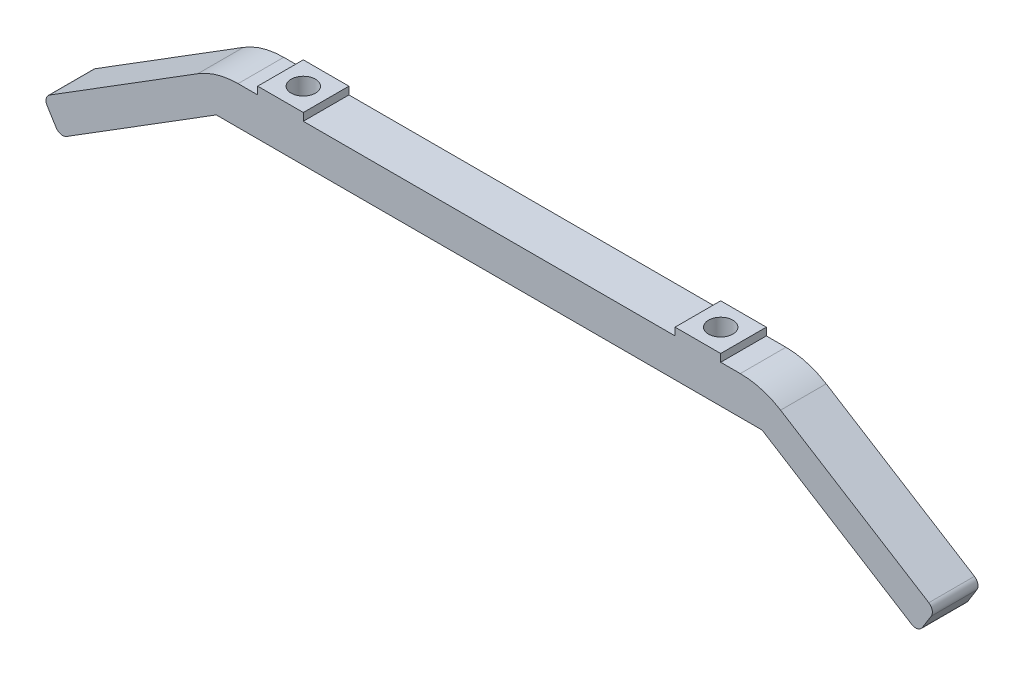
SolidWorks part; units mm, degrees
ref_plane "前视基准面" through (0, 0, 0) normal (0, 0, 1) x (1, 0, 0)
ref_plane "上视基准面" through (0, 0, 0) normal (0, 1, 0) x (1, 0, 0)
ref_plane "右视基准面" through (0, 0, 0) normal (1, 0, 0) x (0, 0, -1)
sketch "草图1" plane through (0, 0, 0) normal (0, 0, 1) x (1, 0, 0)
  line L0 (0, 148.5) -> (0, -94.9538) construction
  line L1 (105, -148.5) -> (-105, -148.5) construction
  line L2 (105, -148.5) -> (105, 148.5) construction
  line L3 (105, 148.5) -> (-105, 148.5) construction
  line L4 (-105, -148.5) -> (-105, 148.5) construction
  line L5 (105, -148.5) -> (-105, 148.5) construction
  line L6 (105, 148.5) -> (-105, -148.5) construction
  line L7 (35.8892, 121.6645) -> (-35.8892, 121.6645)
  line L8 (-35.8892, 121.6645) -> (-66.9017, 102.292)
  line L9 (-75, 40.9339) -> (-75, 31.2613)
  line L10 (-66.9017, 102.292) -> (-66.9017, 52.8701)
  line L11 (75, 40.9339) -> (75, 31.2613)
  line L12 (66.9017, 102.292) -> (66.9017, 52.8701)
  line L13 (35.8892, 121.6645) -> (66.9017, 102.292)
  line L14 (-75, 31.2613) -> (75, 31.2613)
  line L15 (-60, -148.5) -> (-60, -91.8129)
  line L16 (-75, 23.94) -> (75, 23.94)
  line L17 (-75, 23.94) -> (-75, 10.5626)
  line L18 (-38.8455, -105.5906) -> (-66.4608, -113.7617)
  line L19 (-66.4608, -113.7617) -> (-70.1743, -102.7328)
  line L20 (75, 23.94) -> (75, 10.5626)
  line L21 (66.4608, -113.7617) -> (70.1743, -102.7328)
  line L22 (38.8455, -105.5906) -> (66.4608, -113.7617)
  line L23 (-105, 93.0519) -> (105, 93.0519)
  line L24 (-105, 63.0519) -> (105, 63.0519)
  line L25 (-105, -90.0629) -> (-70.5337, -90.0629)
  line L26 (-105, -60.0629) -> (-67.4027, -60.0629)
  line L27 (60, -148.5) -> (60, 148.5)
  line L28 (-60, -58.3129) -> (-45, -58.3129)
  line L29 (-60, -61.8129) -> (-45, -61.8129)
  line L30 (-36, -58.3129) -> (-21, -58.3129)
  line L31 (-36, -61.8129) -> (-21, -61.8129)
  line L32 (-60, -88.3129) -> (-45, -88.3129)
  line L33 (-60, -91.8129) -> (-45, -91.8129)
  line L34 (-36, -88.3129) -> (-21, -88.3129)
  line L35 (-36, -91.8129) -> (-21, -91.8129)
  line L36 (-60, -58.3129) -> (-60, 148.5)
  line L37 (-19.25, -90.0629) -> (105, -90.0629)
  line L38 (-19.25, -60.0629) -> (19.25, -60.0629)
  line L39 (-60, -88.3129) -> (-60, -61.8129)
  line L40 (21, -58.3129) -> (36, -58.3129)
  line L41 (45, -58.3129) -> (60, -58.3129)
  line L42 (60, -61.8129) -> (45, -61.8129)
  line L43 (36, -61.8129) -> (21, -61.8129)
  line L44 (21, -88.3129) -> (36, -88.3129)
  line L45 (21, -91.8129) -> (36, -91.8129)
  line L46 (45, -88.3129) -> (60, -88.3129)
  line L47 (45, -91.8129) -> (60, -91.8129)
  line L48 (37.75, -60.0629) -> (43.25, -60.0629)
  line L49 (58.25, -60.0629) -> (105, -60.0629)
  line L50 (-60, 94.8019) -> (-45, 94.8019)
  line L51 (-36, 94.8019) -> (-21, 94.8019)
  line L52 (-60, 91.3019) -> (-45, 91.3019)
  line L53 (-36, 91.3019) -> (-21, 91.3019)
  line L54 (-60, 64.8019) -> (-45, 64.8019)
  line L55 (-60, 61.3019) -> (-45, 61.3019)
  line L56 (-36, 64.8019) -> (-21, 64.8019)
  line L57 (-36, 61.3019) -> (-21, 61.3019)
  line L58 (21, 94.8019) -> (36, 94.8019)
  line L59 (21, 91.3019) -> (36, 91.3019)
  line L60 (45, 94.8019) -> (60, 94.8019)
  line L61 (45, 91.3019) -> (60, 91.3019)
  line L62 (21, 61.3019) -> (36, 61.3019)
  line L63 (21, 64.8019) -> (36, 64.8019)
  line L64 (45, 61.3019) -> (60, 61.3019)
  line L65 (45, 64.8019) -> (60, 64.8019)
  line L66 (-33.1709, -104.7687) -> (33.1709, -104.7687)
  line L67 (0, -104.7687) -> (0, -148.5) construction
  arc A0 (-75, 40.9339) -> (-66.9017, 52.8701) centre (-79.7474, 52.8701) ccw
  arc A1 (75, 40.9339) -> (66.9017, 52.8701) centre (79.7474, 52.8701) cw
  arc A3 (-60, -88.3129) -> (-60, -91.8129) centre (-60, -90.0629) ccw
  arc A4 (-60, -58.3129) -> (-60, -61.8129) centre (-60, -60.0629) ccw
  circle A5 centre (-60, 63.0519) radius 1.75
  circle A6 centre (-60, 93.0519) radius 1.75
  circle A7 centre (60, 93.0519) radius 1.75
  circle A8 centre (60, 63.0519) radius 1.75
  arc A9 (60, -91.8129) -> (60, -88.3129) centre (60, -90.0629) ccw
  arc A10 (60, -61.8129) -> (60, -58.3129) centre (60, -60.0629) ccw
  arc A11 (-36, -58.3129) -> (-36, -61.8129) centre (-36, -60.0629) ccw
  arc A12 (-36, -88.3129) -> (-36, -91.8129) centre (-36, -90.0629) ccw
  arc A13 (36, -61.8129) -> (36, -58.3129) centre (36, -60.0629) ccw
  arc A14 (36, -91.8129) -> (36, -88.3129) centre (36, -90.0629) ccw
  arc A15 (-45, -61.8129) -> (-45, -58.3129) centre (-45, -60.0629) ccw
  arc A16 (-21, -61.8129) -> (-21, -58.3129) centre (-21, -60.0629) ccw
  arc A17 (-45, -91.8129) -> (-45, -88.3129) centre (-45, -90.0629) ccw
  arc A18 (-21, -91.8129) -> (-21, -88.3129) centre (-21, -90.0629) ccw
  arc A19 (45, -58.3129) -> (45, -61.8129) centre (45, -60.0629) ccw
  arc A20 (21, -58.3129) -> (21, -61.8129) centre (21, -60.0629) ccw
  arc A21 (21, -88.3129) -> (21, -91.8129) centre (21, -90.0629) ccw
  arc A22 (45, -88.3129) -> (45, -91.8129) centre (45, -90.0629) ccw
  circle A23 centre (-36, 93.0519) radius 1.75
  circle A24 centre (-36, 63.0519) radius 1.75
  circle A25 centre (36, 93.0519) radius 1.75
  circle A26 centre (36, 63.0519) radius 1.75
  circle A27 centre (-45, 93.0519) radius 1.75
  circle A28 centre (-21, 93.0519) radius 1.75
  circle A29 centre (-45, 63.0519) radius 1.75
  circle A30 centre (-21, 63.0519) radius 1.75
  circle A31 centre (21, 93.0519) radius 1.75
  circle A32 centre (21, 63.0519) radius 1.75
  circle A33 centre (45, 93.0519) radius 1.75
  circle A34 centre (45, 63.0519) radius 1.75
  arc A35 (33.1709, -104.7687) -> (38.8455, -105.5906) centre (33.1709, -124.7687) cw
  arc A36 (-33.1709, -104.7687) -> (-38.8455, -105.5906) centre (-33.1709, -124.7687) ccw
  spline S0 degree 3 poles (-75, 10.5626) (-72.6959, 1.9073) (-70.3396, -13.3728) (-67.1028, -43.6255) (-66.7657, -72.9327) (-71.8903, -95.1489) (-70.1743, -102.7328) knots 0 0 0 0 0.235247 0.406294 0.801186 1 1 1 1
  spline S1 degree 3 poles (75, 10.5626) (72.6959, 1.9073) (70.3396, -13.3728) (67.1028, -43.6255) (66.7657, -72.9327) (71.8903, -95.1489) (70.1743, -102.7328) knots 0 0 0 0 0.235247 0.406294 0.801186 1 1 1 1
  point P0 (0, 0)
  point P27 (0, 121.6645)
  point P42 (0, -94.0966)
  dimension "D1" = 60
  dimension "D4" = 20
  dimension "D5" = 24
  dimension "D7" = 24
  dimension "D9" = 15
  dimension "D10" = 15
  dimension "D13" = 24
  dimension "D17" = 15
  dimension "D2" = 30
  dimension "D3" = 30
  dimension "D6" = 24
  dimension "D8" = 24
  dimension "D11" = 15
  dimension "D12" = 15
  dimension "D14" = 24
  dimension "D15" = 24
  dimension "D16" = 24
  dimension "D18" = 15
  dimension "D19" = 15
  dimension "D20" = 15
  dimension "D21" = 15
  dimension "D22" = 15
  dimension "D23" = 15
  dimension "D24" = 15
  dimension "D25" = 15
  dimension "D26" = 15
  dimension "D27" = 15
  dimension "D28" = 15
  dimension "D29" = 3.5
  dimension "D30" = 3.5
  dimension "D31" = 3.5
extrude "凸台-拉伸1" add sketch "草图1" along normal blind 3
sketch "草图7" plane through (0, 0, 0) normal (0, 0, -1) x (-1, 0, 0)
  line L0 (0, 121.6645) -> (0, -104.7687) construction
  line L1 (-35.8892, 121.6645) -> (35.8892, 121.6645) construction
  line L2 (33.1709, -104.7687) -> (-33.1709, -104.7687) construction
  line L3 (0, 41.2613) -> (-21, 41.2613) construction
  line L4 (0, 41.2613) -> (21, 41.2613) construction
  line L5 (0, 13.94) -> (-21, 13.94) construction
  line L6 (0, 13.94) -> (21, 13.94) construction
  line L7 (75, 23.94) -> (-75, 23.94) construction
  line L8 (75, 31.2613) -> (-75, 31.2613) construction
  circle A0 centre (-21, 41.2613) radius 2.25
  circle A1 centre (21, 41.2613) radius 2.25
  circle A2 centre (-21, 13.94) radius 2.25
  circle A3 centre (21, 13.94) radius 2.25
  dimension "D1" = 10
  dimension "D2" = 10
extrude "切除-拉伸2" cut sketch "草图7" against normal through all
sketch "草图8" plane through (0, 0, 3) normal (0, 0, 1) x (1, 0, 0)
  line L0 (0, 121.6645) -> (0, -1.9696) construction
  line L1 (35.8892, 121.6645) -> (-35.8892, 121.6645) construction
  line L2 (-33.1709, -104.7687) -> (33.1709, -104.7687) construction
  line L3 (-33.409, 20.409) -> (-12.6214, -0.3786)
  line L4 (31.818, -51.182) -> (-31.818, -51.182)
  line L5 (35, -48) -> (35, 15.6418)
  line L8 (-35, 18.818) -> (-12.6214, -3.5605) construction
  line L9 (-33.409, -52.773) -> (-12.5737, -31.9377)
  line L10 (-36.591, 17.227) -> (-15.8034, -3.5605)
  line L11 (33.4105, 20.4105) -> (12.573, -0.427)
  line L12 (15.803, -3.5609) -> (36.5881, 17.2241)
  line L13 (31.8195, 18.8195) -> (-31.818, 18.818)
  line L14 (-15.8038, -28.8038) -> (-36.591, -49.591)
  line L15 (12.5534, -31.9174) -> (33.409, -52.773)
  line L16 (34.9993, 18.8173) -> (12.6207, -3.5613) construction
  line L17 (0, -30.3951) -> (0, -104.7687) construction
  line L18 (-35, -48) -> (-35, 15.636)
  line L19 (-11.9624, -1.9696) -> (-14.2124, -1.9696) construction
  line L20 (15.8034, -28.8034) -> (36.591, -49.591)
  line L21 (14.2117, -30.3951) -> (11.9607, -30.3951) construction
  line L22 (14.2117, -30.3951) -> (14.2117, -28.1441) construction
  line L23 (14.2117, -1.9696) -> (11.9612, -1.9696) construction
  line L24 (-14.2124, -30.3951) -> (-14.2124, -28.1446) construction
  line L25 (14.2117, -30.3951) -> (12.62, -28.8034) construction
  line L26 (14.2117, -1.9696) -> (12.6204, -3.5609) construction
  line L27 (12.6207, -28.8027) -> (35, -51.182) construction
  line L28 (-12.6215, -3.5606) -> (-14.2124, -1.9696) construction
  line L29 (-14.2124, -4.2196) -> (-14.2124, -1.9696) construction
  line L30 (-12.6214, -28.8034) -> (-35, -51.182) construction
  line L31 (-12.6211, -28.8037) -> (-14.2124, -30.3951) construction
  line L32 (-11.9619, -30.3951) -> (-14.2124, -30.3951) construction
  line L33 (14.2117, -4.2201) -> (14.2117, -1.9696) construction
  line L34 (11.0312, -30.3951) -> (0, -30.3951) construction
  arc A0 (-33.409, 20.409) -> (-36.591, 17.227) centre (-35, 18.818) ccw
  arc A1 (36.5881, 17.2241) -> (33.4105, 20.4105) centre (34.9993, 18.8173) ccw
  arc A2 (-36.591, -49.591) -> (-33.409, -52.773) centre (-35, -51.182) ccw
  arc A3 (33.409, -52.773) -> (36.591, -49.591) centre (35, -51.182) ccw
  arc A4 (-15.8034, -3.5605) -> (-12.6214, -0.3786) centre (-14.2124, -1.9696) ccw
  arc A5 (12.6692, -0.3308) -> (15.803, -3.5609) centre (14.2117, -1.9696) ccw
  arc A6 (-12.6699, -32.0338) -> (-15.8038, -28.8038) centre (-14.2124, -30.3951) ccw
  arc A7 (15.8034, -28.8034) -> (12.6894, -32.0534) centre (14.2117, -30.3951) ccw
  circle A8 centre (-0.0004, -16.1823) radius 8
  point P6 (0, -16.182)
  point P13 (-0.0004, -16.1823)
extrude "切除-拉伸3" cut sketch "草图8" against normal through all
sketch "草图9" plane through (0, 0, 3) normal (0, 0, 1) x (1, 0, 0)
  line L0 (-70.7828, -98.747) -> (70.7828, -98.747) construction
  line L1 (0, -98.747) -> (0, -104.7687) construction
  line L2 (55, -100.497) -> (20, -100.497)
  line L3 (-55, -96.997) -> (-20, -96.997)
  line L4 (-55, -100.497) -> (-20, -100.497)
  line L5 (-33.1709, -104.7687) -> (33.1709, -104.7687) construction
  line L6 (55, -96.997) -> (20, -96.997)
  arc A0 (-55, -96.997) -> (-55, -100.497) centre (-55, -98.747) ccw
  arc A1 (-20, -100.497) -> (-20, -96.997) centre (-20, -98.747) ccw
  arc A2 (20, -100.497) -> (20, -96.997) centre (20, -98.747) cw
  arc A3 (55, -96.997) -> (55, -100.497) centre (55, -98.747) cw
  spline S0 degree 3 poles (-75, 10.5626) (-72.6959, 1.9073) (-70.3396, -13.3728) (-67.1028, -43.6255) (-66.7657, -72.9327) (-71.8903, -95.1489) (-70.1743, -102.7328) knots 0 0 0 0 0.235247 0.406294 0.801186 1 1 1 1 construction
  spline S1 degree 3 poles (75, 10.5626) (72.6959, 1.9073) (70.3396, -13.3728) (67.1028, -43.6255) (66.7657, -72.9327) (71.8903, -95.1489) (70.1743, -102.7328) knots 0 0 0 0 0.235247 0.406294 0.801186 1 1 1 1 construction
  dimension "D1" = 35
  dimension "D2" = 20
extrude "切除-拉伸4" cut sketch "草图9" against normal blind 3
sketch "草图10" plane through (0, 0, 3) normal (0, 0, 1) x (1, 0, 0)
  line L0 (-21, -60.0629) -> (-21, -90.0629) construction
  line L1 (21, -60.0629) -> (21, -90.0629) construction
  line L2 (-21, -75.0629) -> (-17.5, -75.0629) construction
  line L4 (12.5, -80.0629) -> (-12.5, -80.0629)
  line L6 (12.5, -70.0629) -> (-12.5, -70.0629)
  line L11 (17.5, -75.0629) -> (21, -75.0629) construction
  arc A0 (-12.5, -70.0629) -> (-12.5, -80.0629) centre (-12.5, -75.0629) ccw
  arc A1 (12.5, -80.0629) -> (12.5, -70.0629) centre (12.5, -75.0629) ccw
  point P11 (0, -75.0629)
extrude "切除-拉伸5" cut sketch "草图10" against normal blind 3
sketch "草图11" plane through (0, 0, 3) normal (0, 0, 1) x (1, 0, 0)
  line L0 (-21, 93.0519) -> (-21, 63.0519) construction
  line L1 (21, 93.0519) -> (21, 63.0519) construction
  line L2 (-21, 78.0519) -> (-20, 78.0519) construction
  line L4 (15, 73.0519) -> (-15, 73.0519)
  line L6 (15, 83.0519) -> (-15, 83.0519)
  line L10 (20, 78.0519) -> (21, 78.0519) construction
  arc A0 (-15, 83.0519) -> (-15, 73.0519) centre (-15, 78.0519) ccw
  arc A1 (15, 73.0519) -> (15, 83.0519) centre (15, 78.0519) ccw
  point P10 (0, 78.0519)
  dimension "D1" = 30
extrude "切除-拉伸8" cut sketch "草图11" against normal blind 3
sketch "草图12" plane through (0, 0, 3) normal (0, 0, 1) x (1, 0, 0)
  line L0 (0, 121.6645) -> (0, 83.0519) construction
  line L1 (35.8892, 121.6645) -> (-35.8892, 121.6645) construction
  line L2 (15, 83.0519) -> (-15, 83.0519) construction
  circle A0 centre (0, 106.3718) radius 11 construction
  circle A1 centre (0, 106.3718) radius 8 construction
  circle A2 centre (0, 114.3718) radius 1.7
  circle A3 centre (0, 98.3718) radius 1.7
  circle A4 centre (8, 106.3718) radius 1.7
  circle A5 centre (-8, 106.3718) radius 1.7
extrude "切除-拉伸9" cut sketch "草图12" against normal blind 3
sketch "草图13" plane through (0, 0, 3) normal (0, 0, 1) x (1, 0, 0)
  line L0 (0, -104.7687) -> (0, -80.0629) construction
  line L1 (-33.1709, -104.7687) -> (33.1709, -104.7687) construction
  line L2 (-12.5, -80.0629) -> (12.5, -80.0629) construction
  circle A0 centre (0, -92.4158) radius 8 construction
  circle A1 centre (0, -84.4158) radius 1.7
  circle A2 centre (8, -92.4158) radius 1.7
  circle A3 centre (0, -100.4158) radius 1.7
  circle A4 centre (-8, -92.4158) radius 1.7
extrude "切除-拉伸11" cut sketch "草图13" against normal blind 3
sketch "草图14" plane through (0, 0, 3) normal (0, 0, 1) x (1, 0, 0)
  line L0 (0, 23.94) -> (0, -104.7687) construction
  line L1 (-55.4755, 8.9197) -> (-55.4755, -46.0803)
  line L2 (-58.9755, 8.9197) -> (-58.9755, -46.0803)
  line L3 (-75, 23.94) -> (75, 23.94) construction
  line L4 (-33.1709, -104.7687) -> (33.1709, -104.7687) construction
  line L5 (58.9755, 8.9197) -> (58.9755, -46.0803)
  line L6 (55.4755, 8.9197) -> (55.4755, -46.0803)
  arc A0 (-55.4755, 8.9197) -> (-58.9755, 8.9197) centre (-57.2255, 8.9197) ccw
  arc A1 (-58.9755, -46.0803) -> (-55.4755, -46.0803) centre (-57.2255, -46.0803) ccw
  arc A2 (58.9755, -46.0803) -> (55.4755, -46.0803) centre (57.2255, -46.0803) cw
  arc A3 (55.4755, 8.9197) -> (58.9755, 8.9197) centre (57.2255, 8.9197) cw
extrude "切除-拉伸12" cut sketch "草图14" against normal through all
fillet "圆角1" radius 2 2 edges at (75, 31.2613, 1.5) (-75, 31.2613, 1.5)
fillet "圆角2" radius 2 2 edges at (-75, 23.94, 1.5) (75, 23.94, 1.5)
sketch "草图15" plane through (0, 0, 0) normal (0, 0, -1) x (-1, 0, 0)
  line L0 (0, 121.6645) -> (0, 31.2613) construction
  line L1 (-35.8892, 121.6645) -> (35.8892, 121.6645) construction
  line L2 (73, 31.2613) -> (-73, 31.2613) construction
  line L3 (-27.5188, 121.6645) -> (-63.6963, 99.0657) construction
  line L4 (-35.8892, 121.6645) -> (-66.9017, 102.292) construction
  line L5 (-61.1842, 102.4035) -> (-34.7748, 118.9006)
  line L6 (-59.5948, 99.8591) -> (-33.1854, 116.3562)
  line L7 (27.5188, 121.6645) -> (63.6963, 99.0657) construction
  line L8 (59.5948, 99.8591) -> (33.1854, 116.3562)
  line L9 (61.1842, 102.4035) -> (34.7748, 118.9006)
  arc A0 (-61.1842, 102.4035) -> (-59.5948, 99.8591) centre (-60.3895, 101.1313) ccw
  arc A1 (-33.1854, 116.3562) -> (-34.7748, 118.9006) centre (-33.9801, 117.6284) ccw
  arc A2 (33.1854, 116.3562) -> (34.7748, 118.9006) centre (33.9801, 117.6284) cw
  arc A3 (61.1842, 102.4035) -> (59.5948, 99.8591) centre (60.3895, 101.1313) cw
extrude "切除-拉伸13" cut sketch "草图15" against normal through all
sketch "草图16" plane through (0, 0, 0) normal (0, 0, -1) x (-1, 0, 0)
  line L0 (0, 121.6645) -> (0, 31.2613) construction
  line L1 (-35.8892, 121.6645) -> (35.8892, 121.6645) construction
  line L2 (73, 31.2613) -> (-73, 31.2613) construction
  line L3 (-21, 41.2613) -> (-66.71, 41.2613) construction
  line L4 (-61.517, 42.7613) -> (-32.0563, 42.7613)
  line L5 (-61.517, 39.7613) -> (-32.0563, 39.7613)
  line L6 (21, 41.2613) -> (66.71, 41.2613) construction
  line L7 (61.517, 39.7613) -> (32.0563, 39.7613)
  line L8 (61.517, 42.7613) -> (32.0563, 42.7613)
  arc A0 (-61.517, 42.7613) -> (-61.517, 39.7613) centre (-61.517, 41.2613) ccw
  arc A1 (-32.0563, 39.7613) -> (-32.0563, 42.7613) centre (-32.0563, 41.2613) ccw
  arc A2 (32.0563, 39.7613) -> (32.0563, 42.7613) centre (32.0563, 41.2613) cw
  arc A3 (61.517, 42.7613) -> (61.517, 39.7613) centre (61.517, 41.2613) cw
extrude "切除-拉伸14" cut sketch "草图16" against normal through all
sketch "草图17" plane through (0, 0, 0) normal (0, 0, -1) x (-1, 0, 0)
  text T0 "Y" font "黑体" height in points 72
extrude "切除-拉伸15" cut sketch "草图17" against normal through all
sketch "草图18" plane through (0, 0, 0) normal (0, 0, -1) x (-1, 0, 0)
  text T0 "H" font "黑体" height in points 72
extrude "切除-拉伸16" cut sketch "草图18" against normal through all
sketch "草图19" plane through (0, 0, 0) normal (0, 0, -1) x (-1, 0, 0)
  line L1 (-87.3022, 27.5246) -> (87.3022, 27.5246)
  line L2 (-87.3022, 27.5246) -> (-87.3022, -126.2702)
  line L3 (-87.3022, -126.2702) -> (87.3022, -126.2702)
  line L4 (87.3022, 27.5246) -> (87.3022, -126.2702)
extrude "切除-拉伸17" cut sketch "草图19" against normal blind 10
ref_plane "基准面1" through (0, 0, 13) normal (0, 0, 1) x (1, 0, 0)
sketch "草图20" plane through (0, 0, 13) normal (0, 0, 1) x (1, 0, 0)
  line L0 (-13, 106.3718) -> (-13, 129.6645) construction
  line L1 (13, 106.3718) -> (13, 129.6645) construction
  line L2 (35.8892, 121.6645) -> (-35.8892, 121.6645) construction
  line L4 (-13, 106.3718) -> (-13, 129.6645)
  line L5 (-13, 129.6645) -> (13, 129.6645)
  line L6 (13, 106.3718) -> (13, 129.6645)
  circle A0 centre (0, 98.3718) radius 1.7 construction
  circle A1 centre (-8, 106.3718) radius 1.7 construction
  circle A2 centre (8, 106.3718) radius 1.7 construction
  circle A3 centre (0, 114.3718) radius 1.7 construction
  circle A4 centre (0, 98.3718) radius 1.7
  circle A5 centre (-8, 106.3718) radius 1.7
  circle A6 centre (8, 106.3718) radius 1.7
  circle A7 centre (0, 114.3718) radius 1.7
  arc A8 (-13, 106.3718) -> (13, 106.3718) centre (0, 106.3718) ccw
  circle A9 centre (0, 106.3718) radius 2.9291
  dimension "D1" = 8
extrude "凸台-拉伸2" add sketch "草图20" along normal blind 5 separate body
sketch "草图21" plane through (0, 0, 18) normal (0, 0, 1) x (1, 0, 0)
  line L0 (0, 129.6645) -> (0, 124.6645) construction
  line L1 (13, 129.6645) -> (-13, 129.6645) construction
  line L3 (35.8892, 124.6647) -> (-35.8892, 124.6647)
  line L4 (35.8892, 124.6647) -> (35.8892, 129.6644)
  line L5 (35.8892, 129.6644) -> (-35.8892, 129.6644)
  line L6 (-35.8892, 124.6647) -> (-35.8892, 129.6644)
  line L7 (35.8892, 124.6647) -> (-35.8892, 129.6644) construction
  line L8 (35.8892, 129.6644) -> (-35.8892, 124.6647) construction
  point P5 (0, 127.1645)
extrude "凸台-拉伸3" add sketch "草图21" against normal blind 5
sketch "草图22" plane through (0, 0, 18) normal (0, 0, 1) x (1, 0, 0)
  line L0 (-24.4446, 124.6647) -> (-13, 116.6647)
  line L1 (-35.8892, 124.6647) -> (-13, 124.6647) construction
  line L2 (0, 93.3718) -> (0, 129.6645) construction
  line L3 (13, 129.6645) -> (-13, 129.6645) construction
  line L4 (24.4446, 124.6647) -> (13, 116.6647)
  line L5 (-24.4446, 124.6647) -> (-13, 124.6647)
  line L6 (-13, 124.6647) -> (-13, 116.6647)
  line L7 (24.4446, 124.6647) -> (13, 124.6647)
  line L8 (13, 124.6647) -> (13, 116.6647)
  arc A0 (-13, 106.3718) -> (13, 106.3718) centre (0, 106.3718) ccw construction
  dimension "D1" = 8
extrude "凸台-拉伸4" add sketch "草图22" against normal up to surface (5 mm away) up to face at (0, 123.0324, 13)
fillet "圆角3" radius 10 4 edges at (13, 116.6647, 15.5) (24.4446, 124.6647, 15.5) (-13, 116.6647, 15.5) (-24.4446, 124.6647, 15.5)
sketch "草图23" plane through (0, 0, 13) normal (0, 0, -1) x (-1, 0, 0)
  line L1 (-35.8892, 129.6644) -> (35.8892, 129.6644)
  line L2 (-35.8892, 129.6644) -> (-35.8892, 124.6647)
  line L3 (-35.8892, 124.6647) -> (35.8892, 124.6647)
  line L4 (35.8892, 129.6644) -> (35.8892, 124.6647)
extrude "凸台-拉伸5" add sketch "草图23" along normal blind 5
fillet "圆角4" radius 1 1 edges at (0, 124.6647, 13)
sketch "草图24" plane through (0, 0, 8) normal (0, 0, -1) x (-1, 0, 0)
  line L0 (-35.8892, 127.1645) -> (35.8892, 127.1645) construction
  line L1 (-35.8892, 129.6644) -> (-35.8892, 124.6647) construction
  line L2 (35.8892, 124.6647) -> (35.8892, 129.6644) construction
  line L3 (-35.8892, 124.6647) -> (35.8892, 124.6647) construction
  line L4 (-35.8892, 129.6644) -> (-29.8892, 129.6644)
  line L5 (-35.8892, 129.6644) -> (-35.8892, 124.6647)
  line L6 (-35.8892, 124.6647) -> (-29.8892, 124.6647)
  line L7 (-29.8892, 129.6644) -> (-29.8892, 124.6647)
  line L9 (35.8892, 129.6644) -> (29.8892, 129.6644)
  line L10 (35.8892, 129.6644) -> (35.8892, 124.6647)
  line L11 (35.8892, 124.6647) -> (29.8892, 124.6647)
  line L12 (29.8892, 129.6644) -> (29.8892, 124.6647)
extrude "凸台-拉伸7" add sketch "草图24" along normal blind 55
sketch "草图25" plane through (0, 129.6644, 0) normal (0, 1, 0) x (1, 0, 0)
  line L0 (-29.8892, 2) -> (-13.8892, -8)
  line L1 (-29.8892, 47) -> (-29.8892, -8) construction
  line L2 (-29.8892, -8) -> (29.8892, -8) construction
  line L3 (0, -8) -> (0, 42) construction
  line L4 (-29.8892, 2) -> (-29.8892, -8)
  line L5 (-29.8892, -8) -> (-13.8892, -8)
  line L6 (29.8892, -8) -> (13.8892, -8)
  line L7 (29.8892, 2) -> (29.8892, -8)
  line L8 (29.8892, 2) -> (13.8892, -8)
  dimension "D1" = 10
  dimension "D2" = 16
extrude "凸台-拉伸8" add sketch "草图25" against normal up to surface (4.9997 mm away) up to face at (0, 124.6647, -6.3333)
fillet "圆角5" radius 8 4 edges at (13.8892, 127.1645, 8) (29.8892, 127.1645, -2) (-13.8892, 127.1645, 8) (-29.8892, 127.1645, -2)
fillet "圆角6" radius 12 2 edges at (35.8892, 127.1645, 18) (-35.8892, 127.1645, 18)
sketch "草图26" plane through (0, 129.6644, 0) normal (0, 1, 0) x (1, 0, 0)
  line L0 (0, -18) -> (0, 27) construction
  line L1 (13, -18) -> (-13, -18) construction
sketch "草图27" plane through (0, 129.6644, 0) normal (0, 1, 0) x (1, 0, 0)
  line L0 (0, 27) -> (-29.8892, 27) construction
  line L1 (-29.8892, 6.434) -> (-24.8892, 6.434)
  line L2 (-29.8892, 6.434) -> (-29.8892, 12.434)
  line L3 (-29.8892, 12.434) -> (-24.8892, 12.434)
  line L4 (-24.8892, 6.434) -> (-24.8892, 12.434)
  line L9 (-29.8892, 47) -> (-29.8892, 6.434) construction
  line L10 (0, 27) -> (0, -18) construction
  line L11 (-29.8892, 27) -> (-24.8892, 27)
  line L12 (-29.8892, 27) -> (-29.8892, 21)
  line L13 (-29.8892, 21) -> (-24.8892, 21)
  line L14 (-24.8892, 27) -> (-24.8892, 21)
  line L15 (24.8892, 27) -> (24.8892, 21)
  line L16 (29.8892, 21) -> (24.8892, 21)
  line L17 (29.8892, 27) -> (29.8892, 21)
  line L18 (29.8892, 27) -> (24.8892, 27)
  line L23 (24.8892, 6.434) -> (24.8892, 12.434)
  line L24 (29.8892, 12.434) -> (24.8892, 12.434)
  line L25 (29.8892, 6.434) -> (29.8892, 12.434)
  line L26 (29.8892, 6.434) -> (24.8892, 6.434)
  line L27 (-35.8892, 47) -> (-29.8892, 47) construction
  line L28 (-29.8892, 47) -> (-24.8892, 47)
  line L29 (-29.8892, 47) -> (-29.8892, 41)
  line L30 (-29.8892, 41) -> (-24.8892, 41)
  line L31 (-24.8892, 47) -> (-24.8892, 41)
  line L33 (29.8892, 47) -> (24.8892, 47)
  line L34 (29.8892, 47) -> (29.8892, 41)
  line L35 (29.8892, 41) -> (24.8892, 41)
  line L36 (24.8892, 47) -> (24.8892, 41)
extrude "凸台-拉伸9" add sketch "草图27" against normal up to surface (4.9997 mm away) up to face at (0, 124.6647, -5.306)
fillet "圆角7" radius 1 10 edges at (29.8892, 127.1645, -6.434) (29.8892, 127.1645, -12.434) (29.8892, 127.1645, -21) (29.8892, 127.1645, -27) (29.8892, 127.1645, -41) (-29.8892, 127.1645, -41) (-29.8892, 127.1645, -27) (-29.8892, 127.1645, -21) (-29.8892, 127.1645, -12.434) (-29.8892, 127.1645, -6.434)
fillet "圆角8" radius 1 10 edges at (24.8892, 127.1645, -41) (-24.8892, 127.1645, -41) (24.8892, 127.1645, -27) (24.8892, 127.1645, -21) (24.8892, 127.1645, -12.434) (24.8892, 127.1645, -6.434) (-24.8892, 127.1645, -6.434) (-24.8892, 127.1645, -12.434) (-24.8892, 127.1645, -21) (-24.8892, 127.1645, -27)
fillet "圆角9" radius 1 4 edges at (35.8892, 127.1645, -47) (24.8892, 127.1645, -47) (-35.8892, 127.1645, -47) (-24.8892, 127.1645, -47)
sketch "草图28" plane through (0, 129.6644, 0) normal (0, 1, 0) x (1, 0, 0)
  line L0 (-24.8892, 44) -> (-35.8892, 44) construction
  line L1 (-24.8892, 42) -> (-24.8892, 46) construction
  line L2 (-35.8892, 46) -> (-35.8892, -6) construction
  line L3 (-27.4458, 44) -> (-27.4458, 47.064) construction
  line L4 (-27.4458, 44) -> (-27.4458, 3.3304) construction
  line L5 (-24.8892, 24) -> (-35.8892, 24) construction
  line L6 (-24.8892, 22) -> (-24.8892, 26) construction
  line L7 (-24.8892, 9.434) -> (-35.8892, 9.434) construction
  line L8 (-24.8892, 7.434) -> (-24.8892, 11.434) construction
  line L9 (0, -8) -> (0, 47.064) construction
  line L10 (-11.5948, -8) -> (11.5948, -8) construction
  line L11 (27.4458, 44) -> (27.4458, 3.3304) construction
  line L12 (27.4458, 44) -> (27.4458, 47.064) construction
  circle A0 centre (-27.4458, 44) radius 1.6
  circle A1 centre (-27.4458, 24) radius 1.6
  circle A2 centre (-27.4458, 9.434) radius 1.6
  circle A3 centre (27.4458, 9.434) radius 1.6
  circle A4 centre (27.4458, 24) radius 1.6
  circle A5 centre (27.4458, 44) radius 1.6
extrude "切除-拉伸19" cut sketch "草图28" against normal blind 50
sketch "草图29" plane through (0, 0, 0) normal (0, 0, -1) x (-1, 0, 0)
  line L1 (-86.8175, 27.2362) -> (87.5527, 27.2362)
  line L2 (-86.8175, 27.2362) -> (-86.8175, 122.5914)
  line L3 (-86.8175, 122.5914) -> (87.5527, 122.5914)
  line L4 (87.5527, 27.2362) -> (87.5527, 122.5914)
ref_plane "基准面2" through (0, 0, -6.434) normal (0, 0, 1) x (1, 0, 0)
sketch "草图32" plane through (0, 0, -6.434) normal (0, 0, 1) x (1, 0, 0)
  line L0 (35.8892, 134.6644) -> (35.8892, 141.3433) construction
  line L1 (-35.8892, 129.6644) -> (-56.4167, 116.8415)
  line L2 (-35.8892, 129.6644) -> (35.8892, 129.6644)
  line L4 (-35.8892, 134.6644) -> (35.8892, 134.6644)
  line L6 (-35.8892, 134.6644) -> (-58.6633, 120.4381)
  line L7 (-35.8892, 121.6645) -> (-66.9017, 102.292) construction
  line L8 (-56.4167, 116.8415) -> (-58.6633, 120.4381)
  line L9 (0, 129.6644) -> (0, 98.3718) construction
  line L10 (56.4167, 116.8415) -> (58.6633, 120.4381)
  line L11 (35.8892, 134.6644) -> (58.6633, 120.4381)
  line L12 (35.8892, 129.6644) -> (56.4167, 116.8415)
extrude "凸台-拉伸10" add sketch "草图32" against normal up to surface (6 mm away) up to face at (-27.3892, 127.1645, -12.434)
sketch "草图33" plane through (0, 124.6647, 0) normal (0, -1, 0) x (1, 0, 0)
  circle A0 centre (-27.4458, -9.434) radius 1.6 construction
  circle A1 centre (27.4458, -9.434) radius 1.6 construction
  circle A2 centre (-27.4458, -9.434) radius 1.6
  circle A3 centre (27.4458, -9.434) radius 1.6
extrude "切除-拉伸21" cut sketch "草图33" against normal through all
sketch "草图34" plane through (0, 0, 0) normal (0, 0, -1) x (-1, 0, 0)
  line L1 (-80.2126, 29.3415) -> (82.6305, 29.3415)
  line L2 (-80.2126, 29.3415) -> (-80.2126, 122.4549)
  line L3 (-80.2126, 122.4549) -> (82.6305, 122.4549)
  line L4 (82.6305, 29.3415) -> (82.6305, 122.4549)
extrude "切除-拉伸22" cut sketch "草图34" against normal blind 10
sketch "草图35" plane through (0, 134.6644, 0) normal (0, 1, 0) x (1, 0, 0)
  line L0 (0, -8) -> (0, 12.434) construction
  line L1 (-11.5948, -8) -> (11.5948, -8) construction
  line L2 (35.8892, 12.434) -> (-35.8892, 12.434) construction
  line L4 (-24.4458, 6.434) -> (-30.4458, 6.434)
  line L5 (-24.4458, 6.434) -> (-24.4458, 12.434)
  line L6 (-24.4458, 12.434) -> (-30.4458, 12.434)
  line L7 (-30.4458, 6.434) -> (-30.4458, 12.434)
  line L8 (-24.4458, 6.434) -> (-30.4458, 12.434) construction
  line L9 (-24.4458, 12.434) -> (-30.4458, 6.434) construction
  line L10 (30.4458, 6.434) -> (24.4458, 6.434)
  line L11 (30.4458, 6.434) -> (30.4458, 12.434)
  line L12 (30.4458, 12.434) -> (24.4458, 12.434)
  line L13 (24.4458, 6.434) -> (24.4458, 12.434)
  line L14 (30.4458, 6.434) -> (24.4458, 12.434) construction
  line L15 (30.4458, 12.434) -> (24.4458, 6.434) construction
  circle A0 centre (-27.4458, 9.434) radius 1.6
  circle A1 centre (27.4458, 9.434) radius 1.6
  point P6 (-27.4458, 9.434)
  point P12 (27.4458, 9.434)
extrude "凸台-拉伸11" add sketch "草图35" along normal blind 1
sketch "草图36" plane through (0, 0, 18) normal (0, 0, 1) x (1, 0, 0)
  line L0 (35.8892, 129.6644) -> (35.8892, 124.6647) construction
  line L1 (-35.8892, 129.6644) -> (35.8892, 129.6644)
  line L2 (-35.8892, 129.6644) -> (-35.8892, 124.6647)
  line L4 (35.8892, 129.6644) -> (35.8892, 124.6647)
  line L5 (27.5932, 124.6647) -> (35.8892, 124.6647) construction
  line L8 (-35.8892, 124.6647) -> (-35.8892, 87.058)
  line L9 (-35.8892, 87.058) -> (35.8892, 87.058)
  line L10 (35.8892, 124.6647) -> (35.8892, 87.058)
extrude "切除-拉伸23" cut sketch "草图36" against normal blind 90
sketch "草图37" plane through (0, 129.6645, 0) normal (0, 1, 0) x (1, 0, 0)
  line L4 (13, -13) -> (-13, -13)
  line L5 (-13, -13) -> (-13, -18)
  line L6 (-13, -18) -> (13, -18)
  line L7 (13, -18) -> (13, -13)
  line L8 (13, -13) -> (-13, -13)
  line L9 (-13, -13) -> (-13, -18)
  line L10 (-13, -18) -> (13, -18)
  line L11 (13, -18) -> (13, -13)
  dimension "D1" = 0
extrude "切除-拉伸24" cut sketch "草图37" against normal blind 90
fillet "圆角10" radius 10 2 edges at (-35.8892, 134.6644, -9.434) (35.8892, 134.6644, -9.434)
fillet "圆角11" radius 1 4 edges at (-56.4167, 116.8415, -9.434) (-58.6633, 120.4381, -9.434) (58.6633, 120.4381, -9.434) (56.4167, 116.8415, -9.434)
